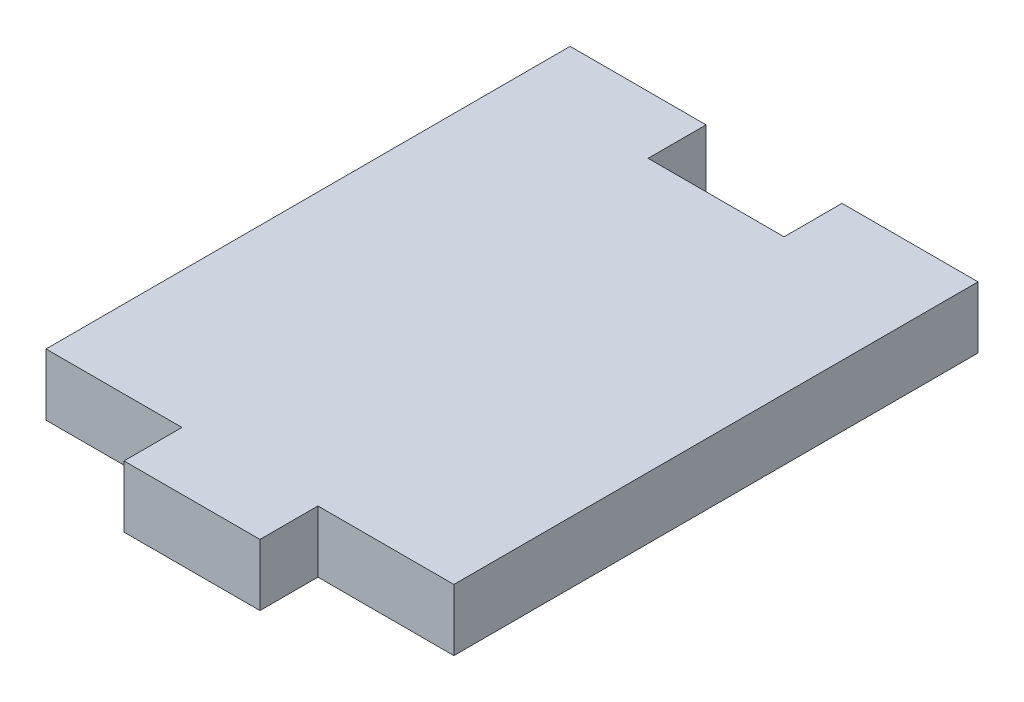
SolidWorks part; units mm, degrees
ref_plane "Front Plane" through (0, 0, 0) normal (0, 0, 1) x (1, 0, 0)
ref_plane "Top Plane" through (0, 0, 0) normal (0, 1, 0) x (1, 0, 0)
ref_plane "Right Plane" through (0, 0, 0) normal (1, 0, 0) x (0, 0, -1)
sketch "Sketch1" plane through (0, 0, 0) normal (0, 1, 0) x (1, 0, 0)
  line L0 (14, 48) -> (14, 53.969)
  line L1 (0, 0) -> (14, 0)
  line L2 (0, 0) -> (0, 48)
  line L3 (14, 48) -> (28, 48)
  line L4 (42, 0) -> (42, 48)
  line L5 (14, 53.969) -> (0, 53.969)
  line L6 (0, 53.969) -> (0, 48)
  line L7 (28, 48) -> (28, 53.969)
  line L8 (28, 53.969) -> (42, 53.969)
  line L9 (42, 53.969) -> (42, 48)
  line L10 (28, 0) -> (42, 0)
  line L12 (14, 0) -> (14, -5.969)
  line L13 (14, -5.969) -> (28, -5.969)
  line L14 (28, 0) -> (28, -5.969)
  dimension "D1" = 42
  dimension "D2" = 48
  dimension "D3" = 5.969
  dimension "D4" = 5.969
extrude "Boss-Extrude1" add sketch "Sketch1" along normal blind 6.35
